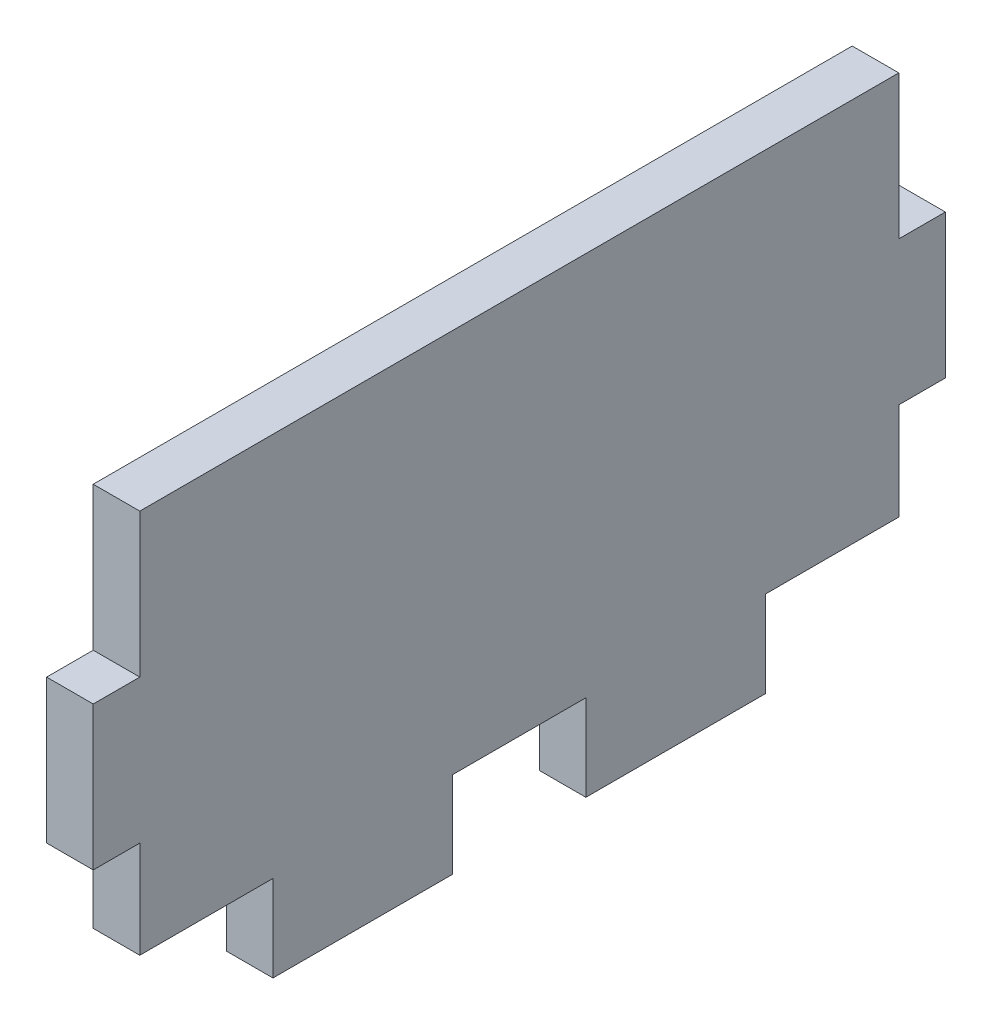
SolidWorks part; units mm, degrees
ref_plane "Ön Düzlem" through (0, 0, 0) normal (0, 0, 1) x (1, 0, 0)
ref_plane "Üst Düzlem" through (0, 0, 0) normal (0, 1, 0) x (1, 0, 0)
ref_plane "Sağ Düzlem" through (0, 0, 0) normal (1, 0, 0) x (0, 0, -1)
sketch "Sketch1" plane through (0, 0, 0) normal (1, 0, 0) x (0, 0, -1)
  line L0 (-24.7, -4.1667) -> (-24.7, 4.1667)
  line L5 (-22, -4.1667) -> (-22, -9.8)
  line L8 (-24.7, 4.1667) -> (-22, 4.1667)
  line L9 (-22, 4.1667) -> (-22, 12.5)
  line L11 (-24.7, -4.1667) -> (-22, -4.1667)
  line L17 (-22, -9.8) -> (-14.28, -9.8)
  line L18 (-3.86, -9.8) -> (3.86, -9.8)
  line L22 (-14.28, -12.5) -> (-14.28, -9.8)
  line L24 (-3.86, -9.8) -> (-3.86, -12.5)
  line L27 (22, 12.5) -> (-22, 12.5)
  line L31 (3.86, -9.8) -> (3.86, -12.5)
  line L32 (14.28, -12.5) -> (14.28, -9.8)
  line L33 (22, -9.8) -> (14.28, -9.8)
  line L34 (24.7, -4.1667) -> (22, -4.1667)
  line L35 (22, 4.1667) -> (22, 12.5)
  line L36 (24.7, 4.1667) -> (22, 4.1667)
  line L38 (22, -4.1667) -> (22, -9.8)
  line L39 (24.7, -4.1667) -> (24.7, 4.1667)
  line L40 (-14.28, -12.5) -> (-14.28, -14.8)
  line L41 (-14.28, -14.8) -> (-3.86, -14.8)
  line L42 (14.28, -14.8) -> (14.28, -12.5)
  line L43 (3.86, -12.5) -> (3.86, -14.8)
  line L44 (-3.86, -12.5) -> (-3.86, -14.8)
  line L45 (3.86, -14.8) -> (14.28, -14.8)
  point P0 (0, 0)
extrude "Boss-Extrude2" add sketch "Sketch1" along normal blind 2.7
